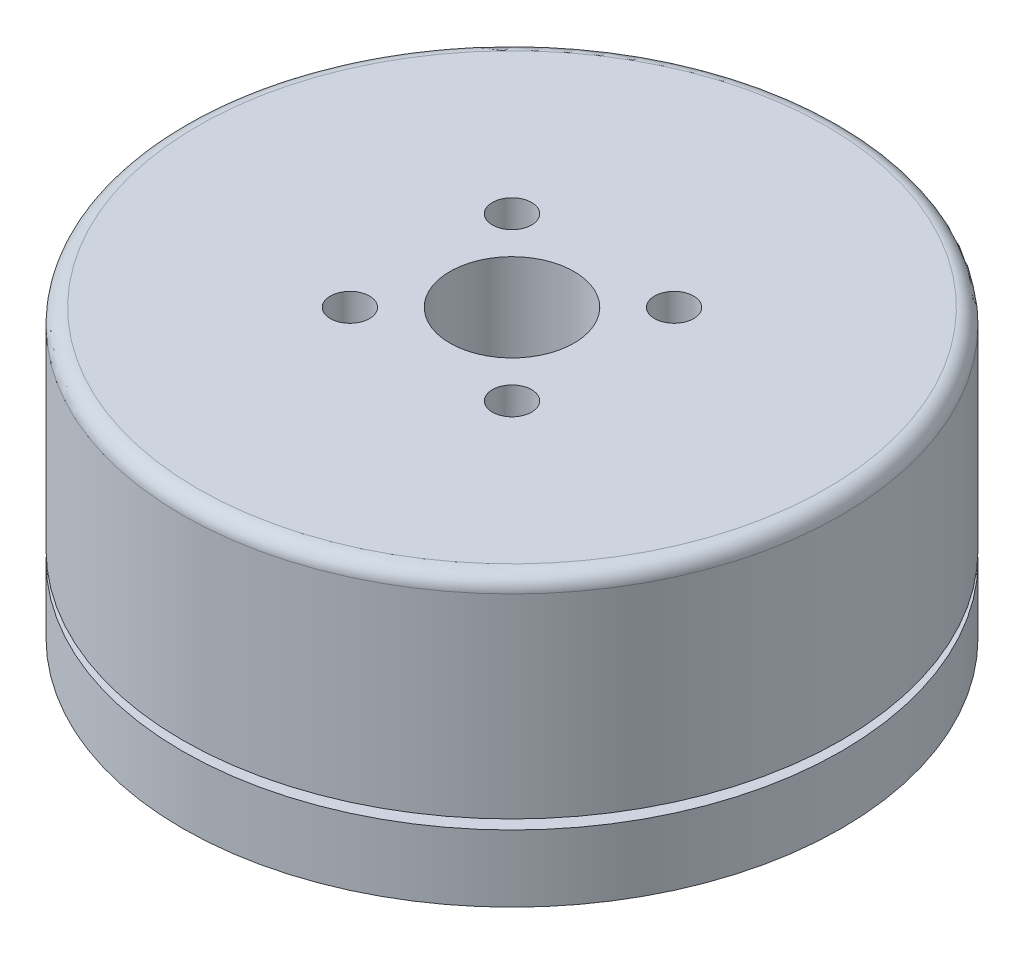
SolidWorks part; units mm, degrees
ref_plane "前视基准面" through (0, 0, 0) normal (0, 0, 1) x (1, 0, 0)
ref_plane "上视基准面" through (0, 0, 0) normal (0, 1, 0) x (1, 0, 0)
ref_plane "右视基准面" through (0, 0, 0) normal (1, 0, 0) x (0, 0, -1)
sketch "草图1" plane through (0, 0, 0) normal (0, 0, 1) x (1, 0, 0)
  line L1 (-6, 0) -> (-6, 1.62)
  line L2 (-6, 1.62) -> (-17.25, 1.62)
  line L3 (-17.25, 1.62) -> (-17.25, 16.62)
  line L5 (0, 44.7193) -> (0, 0) construction
  line L6 (-17.25, 16.62) -> (-3.25, 16.62)
  line L7 (-3.25, 16.62) -> (-3.25, 0)
  line L8 (-3.25, 0) -> (-6, 0)
  dimension "D1" = 6.5
  dimension "D2" = 12
  dimension "D3" = 34.5
  dimension "D4" = 15
  dimension "D5" = 1.62
revolve "旋转1" add sketch "草图1" angle 360 about L5
sketch "草图4" plane through (0, 1.62, 0) normal (0, -1, 0) x (1, 0, 0)
  circle A1 centre (0, 0) radius 17.25
  circle A2 centre (0, 0) radius 17.25
  dimension "D1" = 0
extrude "切除-拉伸-薄壁1" cut sketch "草图4" against normal blind 0.5 from offset 3.5 thin thin type one direction reverse wall 1 offset against normal yes
sketch "草图5" plane through (0, 1.62, 0) normal (0, -1, 0) x (1, 0, 0)
  line L0 (-17.381, 17.381) -> (17.381, -17.381) construction
  line L1 (17.5366, 17.5366) -> (-17.5366, -17.5366) construction
  line L2 (-23.9256, 0) -> (23.5995, 0) construction
  point P5 (0, 0)
  point P9 (0, 0)
  point P11 (-6.7175, 6.7175)
  point P12 (6.7175, -6.7175)
  point P13 (6.7175, 6.7175)
  point P14 (-6.7175, -6.7175)
  dimension "D1" = 45
  dimension "D2" = 19
hole_wizard "M2.5 螺纹孔2" positions "草图7" profile "草图8" tap size "M2.5" standard "GB"
sketch "草图7" plane through (0, 1.62, 0) normal (0, -1, 0) x (-1, 0, 0)
  point P0 (-6.7175, 6.7175)
  point P3 (-6.7175, -6.7175)
  point P6 (6.7175, -6.7175)
  point P9 (6.7175, 6.7175)
sketch "草图8" plane through (6.7175, 1.62, -6.7175) normal (1, 0, 0) x (0, 0, -1)
  line L0 (0, 0) -> (0, 4.1159)
  line L1 (0, 4.1159) -> (1.025, 3.5)
  line L2 (1.025, 3.5) -> (1.025, 0)
  line L5 (1.025, 0) -> (0, 0)
  line L10 (0, 4.1159) -> (-1.025, 3.5) construction
  line L11 (0, -6.35) -> (0, 107.95) construction
  dimension "螺纹孔钻头直径" = 2.05
  dimension "螺纹孔钻头深度" = 3.5
  dimension "导头角度" = 118
cosmetic thread "孔螺蚊线1" parameters "D1"=3.5, "D2"=2.5
cosmetic thread "孔螺蚊线2" parameters "D1"=3.5, "D2"=2.5
cosmetic thread "孔螺蚊线3" parameters "D1"=3.5, "D2"=2.5
cosmetic thread "孔螺蚊线4" parameters "D1"=3.5, "D2"=2.5
sketch "草图9" plane through (0, 1.62, 0) normal (0, -1, 0) x (1, 0, 0)
  line L0 (0, 0) -> (0, -19.9075) construction
  line L2 (-2.9, -15.25) -> (2.9, -15.25)
  line L3 (-2.9, -15.25) -> (-2.9, -13.75)
  line L4 (-2.9, -13.75) -> (2.9, -13.75)
  line L5 (2.9, -15.25) -> (2.9, -13.75)
  circle A0 centre (0, 0) radius 17.25 construction
  point P7 (0, -17.25)
  dimension "D1" = 5.8
  dimension "D2" = 2
  dimension "D3" = 1.5
extrude "凸台-拉伸1" add sketch "草图9" along normal blind 4
sketch "草图10" plane through (0, 16.62, 0) normal (0, 1, 0) x (1, 0, 0)
  line L0 (17.5366, -17.5366) -> (-17.5366, 17.5366) construction
  line L1 (-17.381, -17.381) -> (17.381, 17.381) construction
  line L3 (0, 0) -> (0, -17.9057) construction
  line L4 (-23.9256, 0) -> (23.5995, 0) construction
  line L5 (-23.9256, 0) -> (23.5995, 0) construction
  point P0 (-4.2426, 4.2426)
  point P1 (4.2426, 4.2426)
  point P4 (4.2426, -4.2426)
  point P7 (-4.2426, -4.2426)
  dimension "D1" = 12
hole_wizard "M2.5 螺纹孔1" positions "草图12" profile "草图13" tap size "M2.5" standard "GB"
sketch "草图12" plane through (0, 16.62, 0) normal (0, 1, 0) x (1, 0, 0)
  point P0 (-4.2426, 4.2426)
  point P3 (4.2426, 4.2426)
  point P6 (4.2426, -4.2426)
  point P9 (-4.2426, -4.2426)
sketch "草图13" plane through (-4.2426, 16.62, -4.2426) normal (1, 0, 0) x (0, 0, 1)
  line L0 (0, 0) -> (0, 4.1159)
  line L1 (0, 4.1159) -> (1.025, 3.5)
  line L2 (1.025, 3.5) -> (1.025, 0)
  line L5 (1.025, 0) -> (0, 0)
  line L10 (0, 4.1159) -> (-1.025, 3.5) construction
  line L11 (0, -6.35) -> (0, 107.95) construction
  dimension "螺纹孔钻头直径" = 2.05
  dimension "螺纹孔钻头深度" = 3.5
  dimension "导头角度" = 118
cosmetic thread "孔螺蚊线5" parameters "D1"=5, "D2"=2.5
cosmetic thread "孔螺蚊线6" parameters "D1"=5, "D2"=2.5
cosmetic thread "孔螺蚊线7" parameters "D1"=5, "D2"=2.5
cosmetic thread "孔螺蚊线8" parameters "D1"=5, "D2"=2.5
fillet "圆角1" radius 0.8 1 edges at (0, 16.62, 17.25)
sketch "草图14" plane through (0, 0, 0) normal (0, -1, 0) x (1, 0, 0)
  circle A0 centre (0, 0) radius 4
  dimension "D1" = 8
extrude "切除-拉伸1" cut sketch "草图14" against normal blind 1.3
